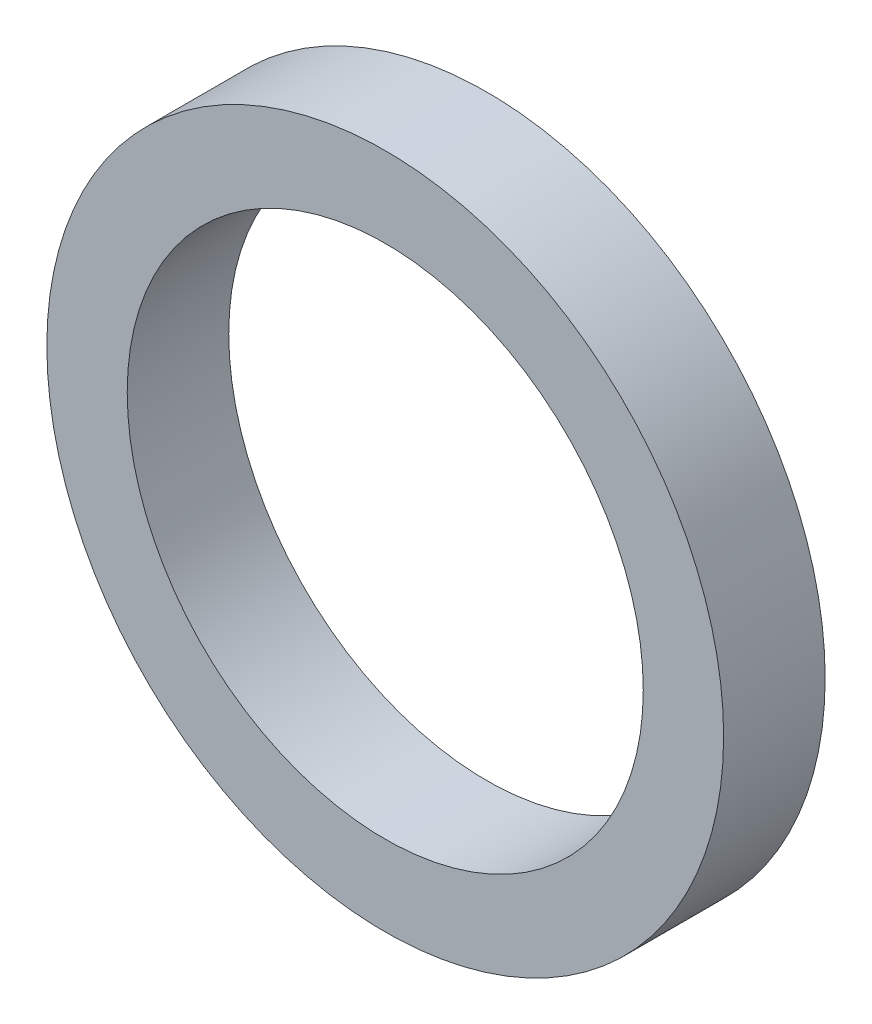
SolidWorks part; units mm, degrees
ref_plane "Front Plane" through (0, 0, 0) normal (0, 0, 1) x (1, 0, 0)
ref_plane "Top Plane" through (0, 0, 0) normal (0, 1, 0) x (1, 0, 0)
ref_plane "Right Plane" through (0, 0, 0) normal (1, 0, 0) x (0, 0, -1)
sketch "Sketch1" plane through (0, 0, 0) normal (0, 0, 1) x (1, 0, 0)
  circle A0 centre (0, 0) radius 20
  dimension "D1" = 40
extrude "Boss-Extrude1" add sketch "Sketch1" along normal blind 6
sketch "Sketch2" plane through (0, 0, 0) normal (0, 0, -1) x (-1, 0, 0)
  circle A0 centre (0, 0) radius 15.25
  dimension "D1" = 30.5
extrude "Cut-Extrude1" cut sketch "Sketch2" against normal through all
